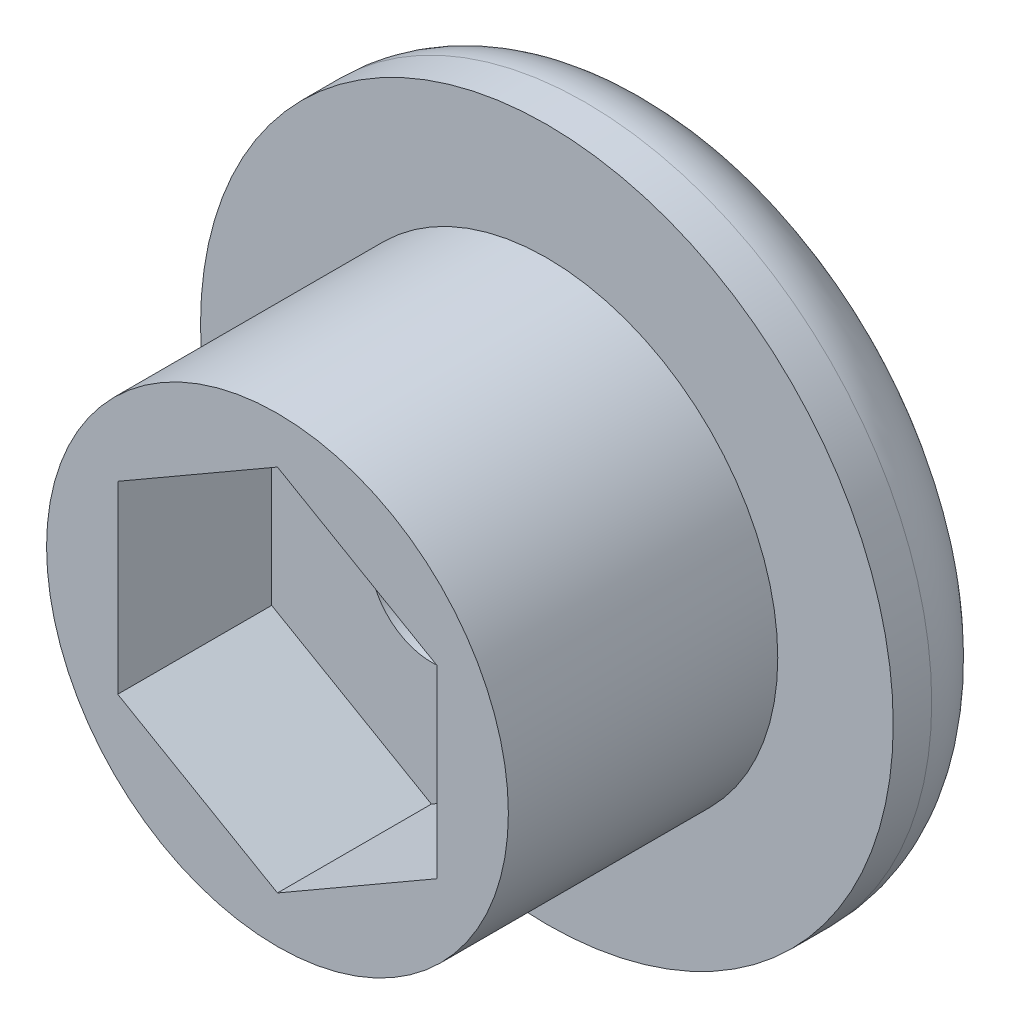
SolidWorks part; units mm, degrees
ref_plane "Alzado" through (0, 0, 0) normal (0, 0, 1) x (1, 0, 0)
ref_plane "Planta" through (0, 0, 0) normal (0, 1, 0) x (1, 0, 0)
ref_plane "Vista lateral" through (0, 0, 0) normal (1, 0, 0) x (0, 0, -1)
sketch "Croquis1" plane through (0, 0, 34.55) normal (0, 0, -1) x (-1, 0, 0)
  line L27 (9.3593, -1.2612) -> (9.3593, -6.0532)
  line L28 (9.3593, -6.0532) -> (13.5093, -8.4492)
  line L29 (13.5093, -8.4492) -> (17.6593, -6.0532)
  line L30 (17.6593, -6.0532) -> (17.6593, -1.2612)
  line L31 (17.6593, -1.2612) -> (13.5093, 1.1348)
  line L32 (13.5093, 1.1348) -> (9.3593, -1.2612)
  line L33 (9.3593, -1.2612) -> (9.3593, -6.0532)
  line L34 (9.3593, -6.0532) -> (13.5093, -8.4492)
  line L35 (13.5093, -8.4492) -> (17.6593, -6.0532)
  line L36 (17.6593, -6.0532) -> (17.6593, -1.2612)
  line L37 (17.6593, -1.2612) -> (13.5093, 1.1348)
  line L38 (13.5093, 1.1348) -> (9.3593, -1.2612)
  circle A0 centre (13.5093, -3.6572) radius 6
  dimension "D2" = 12
  dimension "D1" = 0.15
extrude "Saliente-Extruir1" add sketch "Croquis1" along normal blind 4 from surface
sketch "Croquis2" plane through (0, 0, 37.55) normal (0, 0, -1) x (-1, 0, 0)
  circle A0 centre (13.5093, -3.6572) radius 6 construction
  circle A1 centre (13.5093, -3.6572) radius 6
extrude "Saliente-Extruir2" add sketch "Croquis2" along normal up to surface (3 mm away)
sketch "Croquis3" plane through (0, 0, 34.55) normal (0, 0, -1) x (-1, 0, 0)
  circle A0 centre (13.5093, -3.6572) radius 9
  dimension "D1" = 18
extrude "Saliente-Extruir3" add sketch "Croquis3" along normal blind 3
sketch "Croquis4" plane through (0, 0, 31.55) normal (0, 0, -1) x (-1, 0, 0)
  circle A0 centre (13.5093, -3.6572) radius 1.6
  dimension "D1" = 3.2
extrude "Cortar-Extruir1" cut sketch "Croquis4" against normal blind 11.5
sketch "Croquis5" plane through (0, 0, 31.55) normal (0, 0, -1) x (-1, 0, 0)
  circle A0 centre (13.5093, -3.6572) radius 3
  dimension "D1" = 6
extrude "Cortar-Extruir2" cut sketch "Croquis5" against normal blind 3
fillet "Redondeo1" radius 2 1 edges at (-13.5093, 5.3428, 31.55)
